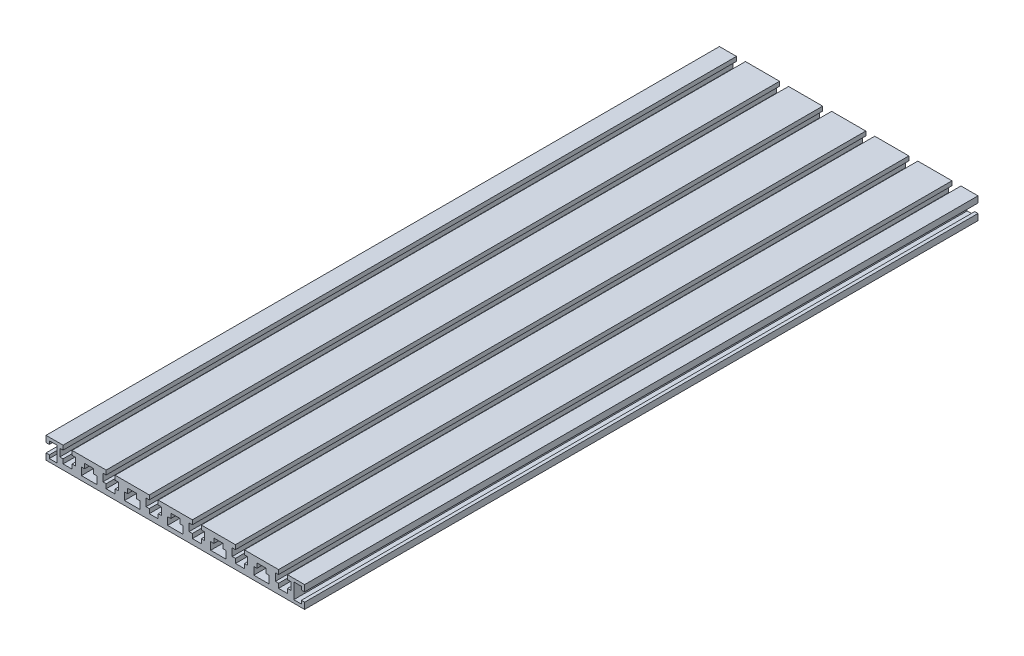
SolidWorks part; units mm, degrees
ref_plane "Front Plane" through (0, 0, 0) normal (0, 0, 1) x (1, 0, 0)
ref_plane "Top Plane" through (0, 0, 0) normal (0, 1, 0) x (1, 0, 0)
ref_plane "Right Plane" through (0, 0, 0) normal (1, 0, 0) x (0, 0, -1)
sketch "Sketch1" plane through (0, 0, 0) normal (0, 0, 1) x (1, 0, 0)
  line L0 (-120, 4.1667) -> (-120, -4.1667)
  line L1 (-120, 10) -> (120, 10)
  line L2 (-120, 10) -> (-120, -10)
  line L3 (-120, -10) -> (120, -10)
  line L4 (120, 10) -> (120, -10)
  line L5 (-120, 10) -> (120, -10) construction
  line L6 (-120, -10) -> (120, 10) construction
  line L7 (-120, -4.1667) -> (-116.9451, -4.1667)
  line L8 (-116.9451, -4.1667) -> (-116.9451, -7.1667)
  line L9 (-116.9451, -7.1667) -> (-109.9451, -7.1667)
  line L10 (-109.9451, -7.1667) -> (-109.9451, 7.1667)
  line L11 (-109.9451, 7.1667) -> (-116.9451, 7.1667)
  line L12 (-116.9451, 7.1667) -> (-116.9451, 4.1667)
  line L13 (-116.9451, 4.1667) -> (-120, 4.1667)
  line L14 (-120, 0) -> (120, 0) construction
  line L15 (-104.1667, 10) -> (-95.8333, 10)
  line L16 (-95.8333, 10) -> (-95.8333, 6)
  line L17 (-95.8333, 6) -> (-92.8333, 6)
  line L18 (-92.8333, 6) -> (-92.8333, -1)
  line L19 (-92.8333, -1) -> (-95.8333, -1)
  line L20 (-95.8333, -1) -> (-95.8333, -5.0939)
  line L21 (-95.8333, -5.0939) -> (-104.1667, -5.0939)
  line L22 (-104.1667, -5.0939) -> (-104.1667, -1)
  line L23 (-104.1667, -1) -> (-107.1667, -1)
  line L24 (-107.1667, -1) -> (-107.1667, 6)
  line L25 (-107.1667, 6) -> (-104.1667, 6)
  line L26 (-104.1667, 6) -> (-104.1667, 10)
  line L27 (-64.1667, 10) -> (-55.8333, 10)
  line L28 (-55.8333, 10) -> (-55.8333, 6)
  line L29 (-55.8333, 6) -> (-52.8333, 6)
  line L30 (-52.8333, 6) -> (-52.8333, -1)
  line L31 (-52.8333, -1) -> (-55.8333, -1)
  line L32 (-55.8333, -1) -> (-55.8333, -5.0939)
  line L33 (-55.8333, -5.0939) -> (-64.1667, -5.0939)
  line L34 (-64.1667, -5.0939) -> (-64.1667, -1)
  line L35 (-64.1667, -1) -> (-67.1667, -1)
  line L36 (-67.1667, -1) -> (-67.1667, 6)
  line L37 (-67.1667, 6) -> (-64.1667, 6)
  line L38 (-64.1667, 6) -> (-64.1667, 10)
  line L39 (-24.1667, 10) -> (-15.8333, 10)
  line L40 (-15.8333, 10) -> (-15.8333, 6)
  line L41 (-15.8333, 6) -> (-12.8333, 6)
  line L42 (-12.8333, 6) -> (-12.8333, -1)
  line L43 (-12.8333, -1) -> (-15.8333, -1)
  line L44 (-15.8333, -1) -> (-15.8333, -5.0939)
  line L45 (-15.8333, -5.0939) -> (-24.1667, -5.0939)
  line L46 (-24.1667, -5.0939) -> (-24.1667, -1)
  line L47 (-24.1667, -1) -> (-27.1667, -1)
  line L48 (-27.1667, -1) -> (-27.1667, 6)
  line L49 (-27.1667, 6) -> (-24.1667, 6)
  line L50 (-24.1667, 6) -> (-24.1667, 10)
  line L51 (15.8333, 10) -> (24.1667, 10)
  line L52 (24.1667, 10) -> (24.1667, 6)
  line L53 (24.1667, 6) -> (27.1667, 6)
  line L54 (27.1667, 6) -> (27.1667, -1)
  line L55 (27.1667, -1) -> (24.1667, -1)
  line L56 (24.1667, -1) -> (24.1667, -5.0939)
  line L57 (24.1667, -5.0939) -> (15.8333, -5.0939)
  line L58 (15.8333, -5.0939) -> (15.8333, -1)
  line L59 (15.8333, -1) -> (12.8333, -1)
  line L60 (12.8333, -1) -> (12.8333, 6)
  line L61 (12.8333, 6) -> (15.8333, 6)
  line L62 (15.8333, 6) -> (15.8333, 10)
  line L63 (55.8333, 10) -> (64.1667, 10)
  line L64 (64.1667, 10) -> (64.1667, 6)
  line L65 (64.1667, 6) -> (67.1667, 6)
  line L66 (67.1667, 6) -> (67.1667, -1)
  line L67 (67.1667, -1) -> (64.1667, -1)
  line L68 (64.1667, -1) -> (64.1667, -5.0939)
  line L69 (64.1667, -5.0939) -> (55.8333, -5.0939)
  line L70 (55.8333, -5.0939) -> (55.8333, -1)
  line L71 (55.8333, -1) -> (52.8333, -1)
  line L72 (52.8333, -1) -> (52.8333, 6)
  line L73 (52.8333, 6) -> (55.8333, 6)
  line L74 (55.8333, 6) -> (55.8333, 10)
  line L75 (95.8333, 10) -> (104.1667, 10)
  line L76 (104.1667, 10) -> (104.1667, 6)
  line L77 (104.1667, 6) -> (107.1667, 6)
  line L78 (107.1667, 6) -> (107.1667, -1)
  line L79 (107.1667, -1) -> (104.1667, -1)
  line L80 (104.1667, -1) -> (104.1667, -5.0939)
  line L81 (104.1667, -5.0939) -> (95.8333, -5.0939)
  line L82 (95.8333, -5.0939) -> (95.8333, -1)
  line L83 (95.8333, -1) -> (92.8333, -1)
  line L84 (92.8333, -1) -> (92.8333, 6)
  line L85 (92.8333, 6) -> (95.8333, 6)
  line L86 (95.8333, 6) -> (95.8333, 10)
  line L87 (-100, -5.0939) -> (-100, 10) construction
  line L88 (0, 10) -> (0, -10) construction
  line L89 (116.9451, 4.1667) -> (120, 4.1667)
  line L90 (116.9451, 7.1667) -> (116.9451, 4.1667)
  line L91 (109.9451, 7.1667) -> (116.9451, 7.1667)
  line L92 (109.9451, -7.1667) -> (109.9451, 7.1667)
  line L93 (116.9451, -7.1667) -> (109.9451, -7.1667)
  line L94 (116.9451, -4.1667) -> (116.9451, -7.1667)
  line L95 (120, -4.1667) -> (116.9451, -4.1667)
  line L96 (120, 4.1667) -> (120, -4.1667)
  line L97 (-87.1667, -6) -> (-72.8333, -6)
  line L98 (-72.8333, -6) -> (-72.8333, 1)
  line L99 (-72.8333, 1) -> (-75.8333, 1)
  line L100 (-75.8333, 1) -> (-75.8333, 5.3622)
  line L101 (-75.8333, 5.3622) -> (-84.1667, 5.3622)
  line L102 (-84.1667, 5.3622) -> (-84.1667, 1)
  line L103 (-84.1667, 1) -> (-87.1667, 1)
  line L104 (-87.1667, 1) -> (-87.1667, -6)
  line L105 (-80, 5.3622) -> (-80, -6) construction
  line L106 (-47.1667, -6) -> (-32.8333, -6)
  line L107 (-32.8333, -6) -> (-32.8333, 1)
  line L108 (-32.8333, 1) -> (-35.8333, 1)
  line L109 (-35.8333, 1) -> (-35.8333, 5.3622)
  line L110 (-35.8333, 5.3622) -> (-44.1667, 5.3622)
  line L111 (-44.1667, 5.3622) -> (-44.1667, 1)
  line L112 (-44.1667, 1) -> (-47.1667, 1)
  line L113 (-47.1667, 1) -> (-47.1667, -6)
  line L114 (-7.1667, -6) -> (7.1667, -6)
  line L115 (7.1667, -6) -> (7.1667, 1)
  line L116 (7.1667, 1) -> (4.1667, 1)
  line L117 (4.1667, 1) -> (4.1667, 5.3622)
  line L118 (4.1667, 5.3622) -> (-4.1667, 5.3622)
  line L119 (-4.1667, 5.3622) -> (-4.1667, 1)
  line L120 (-4.1667, 1) -> (-7.1667, 1)
  line L121 (-7.1667, 1) -> (-7.1667, -6)
  line L122 (32.8333, -6) -> (47.1667, -6)
  line L123 (47.1667, -6) -> (47.1667, 1)
  line L124 (47.1667, 1) -> (44.1667, 1)
  line L125 (44.1667, 1) -> (44.1667, 5.3622)
  line L126 (44.1667, 5.3622) -> (35.8333, 5.3622)
  line L127 (35.8333, 5.3622) -> (35.8333, 1)
  line L128 (35.8333, 1) -> (32.8333, 1)
  line L129 (32.8333, 1) -> (32.8333, -6)
  line L130 (72.8333, -6) -> (87.1667, -6)
  line L131 (87.1667, -6) -> (87.1667, 1)
  line L132 (87.1667, 1) -> (84.1667, 1)
  line L133 (84.1667, 1) -> (84.1667, 5.3622)
  line L134 (84.1667, 5.3622) -> (75.8333, 5.3622)
  line L135 (75.8333, 5.3622) -> (75.8333, 1)
  line L136 (75.8333, 1) -> (72.8333, 1)
  line L137 (72.8333, 1) -> (72.8333, -6)
  point P0 (0, 0)
  dimension "D1" = 240
  dimension "D2" = 20
  dimension "D3" = 14.3333
  dimension "D4" = 3
  dimension "D5" = 7
  dimension "D6" = 14.3333
  dimension "D7" = 3
  dimension "D8" = 7
  dimension "D9" = 4
  dimension "D10" = 20
  dimension "D12" = 14.3333
  dimension "D13" = 7
  dimension "D14" = 3
  dimension "D15" = 4
  dimension "D16" = 20
  dimension "D11" = 6
  dimension "D17" = 5
extrude "Boss-Extrude1" add sketch "Sketch1" along normal blind 625 contours L4 L95 L94 L93 L92 L91 L90 L89 L1 L76 L77 L78 L79 L80 L81 L82 L83 L84 L85 L86 L64 L65 L66 L67 L68 L69 L70 L71 L72 L73 L74 L52 L53 L54 L55 L56 L57 L58 L59 L60 L61 L62 L40 L41 L42 L43 L44
